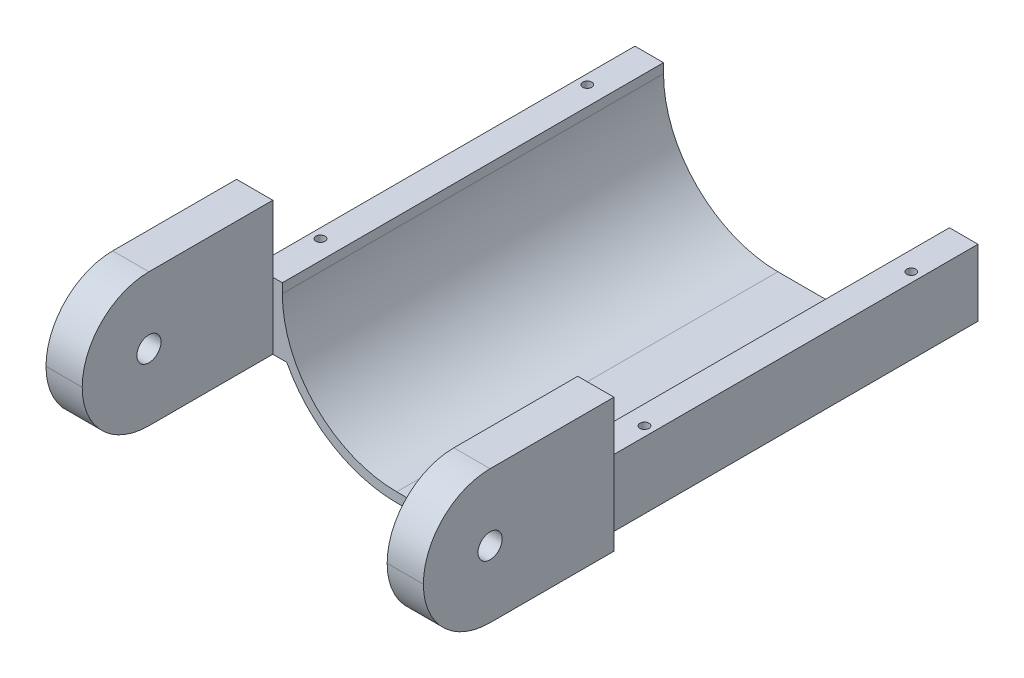
SolidWorks part; units mm, degrees
ref_plane "Front Plane" through (0, 0, 0) normal (0, 0, 1) x (1, 0, 0)
ref_plane "Top Plane" through (0, 0, 0) normal (0, 1, 0) x (1, 0, 0)
ref_plane "Right Plane" through (0, 0, 0) normal (1, 0, 0) x (0, 0, -1)
sketch "Sketch1" plane through (0, 0, 0) normal (0, 0, 1) x (1, 0, 0)
  line L1 (60, 0) -> (90, 0)
  line L2 (0, 60) -> (0, 65)
  line L4 (150, 60) -> (150, 65)
  line L5 (-5, 60) -> (-5, 65)
  line L6 (60, -5) -> (90, -5)
  line L7 (155, 60) -> (155, 65)
  line L8 (-5, 65) -> (155, 65)
  line L10 (-5, 60) -> (-15, 60)
  line L11 (-5, 60) -> (-5, 65)
  line L12 (-5, 65) -> (-15, 65)
  line L13 (-15, 60) -> (-15, 65)
  line L14 (155, 60) -> (165, 60)
  line L15 (155, 60) -> (155, 65)
  line L16 (155, 65) -> (165, 65)
  line L17 (165, 60) -> (165, 65)
  arc A0 (90, 0) -> (150, 60) centre (90, 60) ccw
  arc A1 (60, 0) -> (0, 60) centre (60, 60) cw
  arc A2 (60, -5) -> (-5, 60) centre (60, 60) cw
  arc A3 (90, -5) -> (155, 60) centre (90, 60) ccw
  point P12 (0, 0)
  dimension "D4" = 60
  dimension "D1" = 5
  dimension "D2" = 10
  dimension "D3" = 10
extrude "Boss-Extrude1" add sketch "Sketch1" along normal blind 200 contours L13 L10 L5 L12 | L6 A3 L7 L8 L4 A0 L1 A1 L2 L5 A2 | L14 L17 L16 L7
sketch "Sketch2" plane through (0, 65, 0) normal (0, 1, 0) x (1, 0, 0)
  line L0 (0, 0) -> (-15, 0) construction
  line L1 (-15, -200) -> (-5, -200)
  line L2 (-15, -200) -> (-15, 0)
  line L3 (-15, 0) -> (-5, 0)
  line L4 (-5, -200) -> (-5, 0)
  line L5 (150, -200) -> (165, -200) construction
  line L6 (165, 0) -> (155, 0)
  line L7 (165, 0) -> (165, -200)
  line L8 (165, -200) -> (155, -200)
  line L9 (155, 0) -> (155, -200)
  line L10 (160, -200) -> (160, 0)
  line L11 (160, 0) -> (-10, 0)
  line L12 (-10, 0) -> (-10, -200)
  circle A0 centre (-10, -170) radius 2.3813
  circle A1 centre (-10, -30) radius 2.3813
  circle A2 centre (160, -30) radius 2.3813
  circle A3 centre (160, -170) radius 2.3813
  dimension "D3" = 4.7625
  dimension "D4" = 4.7625
  dimension "D5" = 4.7625
  dimension "D6" = 4.7625
  dimension "D1" = 10
  dimension "D2" = 10
  dimension "D7" = 30
  dimension "D8" = 30
  dimension "D9" = 30
  dimension "D10" = 30
extrude "Cut-Extrude1" cut sketch "Sketch2" against normal blind 200 contours A1 | A0 | A3 | A2
sketch "Sketch3" plane through (0, 0, 200) normal (0, 0, 1) x (1, 0, 0)
  line L1 (-5, 60) -> (-15, 60)
  line L2 (-5, 60) -> (-5, 70)
  line L3 (-5, 70) -> (-15, 70)
  line L4 (-15, 60) -> (-15, 70)
  line L5 (-15, 70) -> (-5, 70)
  line L6 (-15, 70) -> (-15, 100)
  line L7 (-15, 100) -> (-5, 100)
  line L8 (-5, 70) -> (-5, 100)
  line L9 (-15, 60) -> (-5, 60)
  line L10 (-15, 60) -> (-15, 30)
  line L11 (-15, 30) -> (-5, 30)
  line L12 (-5, 60) -> (-5, 30)
  line M4 (-15, 65) -> (-15, 60)
  line M5 (-15, 60) -> (-5, 60)
  line M17 (0, 65) -> (-15, 65)
  dimension "D1" = 10
  dimension "D2" = 30
  dimension "D3" = 30
extrude "Boss-Extrude2" add sketch "Sketch3" along normal blind 100 contours L12 L10 L11 M5 | L2 M5 M17 M4 | L4 L2 L3 M17 | L3 L8 L7 L6
sketch "Sketch4" plane through (-5, 0, 0) normal (1, 0, 0) x (0, 0, -1)
  line L0 (-300, 100) -> (-200, 100) construction
  line L1 (-265.01, 30) -> (-230, 30)
  line L2 (-300, 64.99) -> (-300, 65.01)
  line L3 (-265.01, 100) -> (-230, 100)
  line L4 (-230, 30) -> (-230, 100)
  line L5 (-230, 100) -> (-300, 30)
  circle A0 centre (-265, 65) radius 6.35
  arc A1 (-300, 65.01) -> (-265.01, 100) centre (-265.01, 65.01) cw
  arc A2 (-265.01, 30) -> (-300, 64.99) centre (-265.01, 64.99) cw
  line M6 (-200, 100) -> (-300, 100)
  line M7 (-300, 100) -> (-300, 30)
  line M8 (-300, 30) -> (-200, 30)
  dimension "D2" = 12.7
  dimension "D3" = 34.99
  dimension "D1" = 70
extrude "Cut-Extrude2" cut sketch "Sketch4" against normal blind 100 contours L5 A0 | L5 A0 | A2 L5 M8 | L5 A2 M7 | A1 M7 M6
sketch "Sketch5" plane through (165, 0, 0) normal (1, 0, 0) x (0, 0, -1)
  line L6 (-300, 65.01) -> (-300, 64.99)
  line L7 (-265.01, 30) -> (-200, 30)
  line L8 (-200, 30) -> (-200, 60)
  line L9 (-200, 60) -> (-200, 65)
  line L10 (-200, 65) -> (-200, 100)
  line L11 (-200, 100) -> (-265.01, 100)
  line L12 (-300, 65.01) -> (-300, 64.99)
  line L13 (-265.01, 30) -> (-200, 30)
  line L14 (-200, 30) -> (-200, 60)
  line L15 (-200, 60) -> (-200, 65)
  line L16 (-200, 65) -> (-200, 100)
  line L17 (-200, 100) -> (-265.01, 100)
  circle A0 centre (-265, 65) radius 6.35 construction
  circle A1 centre (-265, 65) radius 6.35
  arc A2 (-265.01, 100) -> (-300, 65.01) centre (-265.01, 65.01) ccw
  arc A3 (-300, 64.99) -> (-265.01, 30) centre (-265.01, 64.99) ccw
  arc A4 (-265.01, 100) -> (-300, 65.01) centre (-265.01, 65.01) ccw
  arc A5 (-300, 64.99) -> (-265.01, 30) centre (-265.01, 64.99) ccw
  dimension "D1" = 0
extrude "Boss-Extrude5" add sketch "Sketch5" against normal up to vertex
sketch "Sketch6" plane through (-5, 0, 0) normal (1, 0, 0) x (0, 0, -1)
  line L6 (-300, 65.01) -> (-300, 64.99)
  line L7 (-265.01, 30) -> (-200, 30)
  line L8 (-200, 30) -> (-200, 60)
  line L9 (-200, 60) -> (-200, 65)
  line L10 (-200, 65) -> (-200, 100)
  line L11 (-200, 100) -> (-265.01, 100)
  line L12 (-300, 65.01) -> (-300, 64.99)
  line L13 (-265.01, 30) -> (-200, 30)
  line L14 (-200, 30) -> (-200, 60)
  line L15 (-200, 60) -> (-200, 65)
  line L16 (-200, 65) -> (-200, 100)
  line L17 (-200, 100) -> (-265.01, 100)
  circle A0 centre (-265, 65) radius 6.35 construction
  circle A1 centre (-265, 65) radius 6.35
  arc A2 (-265.01, 100) -> (-300, 65.01) centre (-265.01, 65.01) ccw
  arc A3 (-300, 64.99) -> (-265.01, 30) centre (-265.01, 64.99) ccw
  arc A4 (-265.01, 100) -> (-300, 65.01) centre (-265.01, 65.01) ccw
  arc A5 (-300, 64.99) -> (-265.01, 30) centre (-265.01, 64.99) ccw
  dimension "D1" = 0
extrude "Boss-Extrude6" add sketch "Sketch6" along normal up to vertex
sketch "Sketch7" plane through (0, 0, 0) normal (0, 0, -1) x (-1, 0, 0)
  line L0 (-165, 30) -> (-145.0237, 30)
  line L1 (-145.0237, 30) -> (5, 30)
  line L2 (5, 30) -> (-150, 30)
  line L4 (15, 60) -> (5, 60)
  line L5 (0, 35) -> (0, 30)
  line L6 (0, 30) -> (15, 30)
  line L7 (15, 30) -> (15, 60)
  line L8 (15, 60) -> (5, 60)
  line L9 (0, 35) -> (0, 30)
  line L10 (0, 30) -> (15, 30)
  line L11 (15, 30) -> (15, 60)
  line L12 (-155, 60) -> (-165, 60)
  line L13 (-165, 60) -> (-165, 30)
  line L14 (-165, 30) -> (-150, 30)
  line L15 (-150, 30) -> (-150, 35)
  line L16 (-155, 60) -> (-165, 60)
  line L17 (-165, 60) -> (-165, 30)
  line L18 (-165, 30) -> (-150, 30)
  line L19 (-150, 30) -> (-150, 35)
  arc A1 (0, 35) -> (5, 60) centre (-60, 60) ccw
  arc A2 (0, 35) -> (5, 60) centre (-60, 60) ccw
  arc A3 (-155, 60) -> (-150, 35) centre (-90, 60) ccw
  arc A4 (-155, 60) -> (-150, 35) centre (-90, 60) ccw
  line M20 (-165, 60) -> (-155, 60)
  arc M21 (-155, 60) -> (-90, -5) centre (-90, 60) ccw
  arc M23 (-60, -5) -> (5, 60) centre (-60, 60) ccw
  line M24 (5, 60) -> (15, 60)
  dimension "D1" = 0
  dimension "D2" = 0
extrude "Boss-Extrude7" add sketch "Sketch7" against normal up to vertex contours L19 L0 M21 | L0 L19 L17 M21 M20 | L9 L1 M23 | L10 L11 L9 L2 M24 M23
sketch "Sketch8" plane through (165, 0, 0) normal (1, 0, 0) x (0, 0, -1)
  line L0 (-200, 100) -> (-200, 30)
  line L6 (-265.01, 30) -> (0, 30)
  line L7 (0, 30) -> (0, 65)
  line L8 (0, 65) -> (-200, 65)
  line L9 (-200, 65) -> (-200, 100)
  line L10 (-200, 100) -> (-265.01, 100)
  line L11 (-300, 65.01) -> (-300, 64.99)
  line L12 (-265.01, 30) -> (0, 30)
  line L13 (0, 30) -> (0, 65)
  line L14 (0, 65) -> (-200, 65)
  line L15 (-200, 65) -> (-200, 100)
  line L16 (-200, 100) -> (-265.01, 100)
  line L17 (-300, 65.01) -> (-300, 64.99)
  circle A0 centre (-265, 65) radius 6.35 construction
  circle A1 centre (-265, 65) radius 6.35
  arc A2 (-265.01, 100) -> (-300, 65.01) centre (-265.01, 65.01) ccw
  arc A3 (-300, 64.99) -> (-265.01, 30) centre (-265.01, 64.99) ccw
  arc A4 (-265.01, 100) -> (-300, 65.01) centre (-265.01, 65.01) ccw
  arc A5 (-300, 64.99) -> (-265.01, 30) centre (-265.01, 64.99) ccw
  line M10 (-265.01, 30) -> (0, 30)
  line M13 (-200, 65) -> (-200, 100)
  line M14 (-200, 100) -> (-265.01, 100)
  arc M15 (-265.01, 100) -> (-300, 65.01) centre (-265.01, 65.01) ccw
  line M16 (-300, 65.01) -> (-300, 64.99)
  arc M17 (-300, 64.99) -> (-265.01, 30) centre (-265.01, 64.99) ccw
  circle M18 centre (-265, 65) radius 6.35
  dimension "D1" = 0
extrude "Boss-Extrude8" add sketch "Sketch8" along normal blind 9 contours L0 M13 M14 M15 M16 M17 M10 M18
sketch "Sketch9" plane through (-15, 0, 0) normal (-1, 0, 0) x (0, 0, 1)
  line L0 (200, 100) -> (200, 30)
  line L6 (0, 65) -> (0, 30)
  line L7 (0, 30) -> (265.01, 30)
  line L8 (300, 64.99) -> (300, 65.01)
  line L9 (265.01, 100) -> (200, 100)
  line L10 (200, 100) -> (200, 65)
  line L11 (200, 65) -> (0, 65)
  line L12 (0, 65) -> (0, 30)
  line L13 (0, 30) -> (265.01, 30)
  line L14 (300, 64.99) -> (300, 65.01)
  line L15 (265.01, 100) -> (200, 100)
  line L16 (200, 100) -> (200, 65)
  line L17 (200, 65) -> (0, 65)
  circle A0 centre (265, 65) radius 6.35 construction
  circle A1 centre (265, 65) radius 6.35
  arc A2 (265.01, 30) -> (300, 64.99) centre (265.01, 64.99) ccw
  arc A3 (300, 65.01) -> (265.01, 100) centre (265.01, 65.01) ccw
  arc A4 (265.01, 30) -> (300, 64.99) centre (265.01, 64.99) ccw
  arc A5 (300, 65.01) -> (265.01, 100) centre (265.01, 65.01) ccw
  line M11 (0, 30) -> (265.01, 30)
  arc M12 (265.01, 30) -> (300, 64.99) centre (265.01, 64.99) ccw
  line M13 (300, 64.99) -> (300, 65.01)
  arc M14 (300, 65.01) -> (265.01, 100) centre (265.01, 65.01) ccw
  line M15 (265.01, 100) -> (200, 100)
  line M16 (200, 100) -> (200, 65)
  circle M18 centre (265, 65) radius 6.35
  dimension "D1" = 0
extrude "Boss-Extrude9" add sketch "Sketch9" along normal blind 9 contours L0 M16 M11 M12 M13 M14 M15 M18
sketch "Sketch10" plane through (150, 0, 0) normal (-1, 0, 0) x (0, 0, 1)
  line L0 (200, 60) -> (200, 65)
  line L8 (0, 65) -> (0, 60)
  line L9 (0, 60) -> (200, 60)
  line L10 (200, 60) -> (200, 30)
  line L11 (200, 30) -> (265.01, 30)
  line L12 (300, 64.99) -> (300, 65.01)
  line L13 (265.01, 100) -> (200, 100)
  line L14 (200, 100) -> (200, 65)
  line L15 (200, 65) -> (0, 65)
  line L16 (0, 65) -> (0, 60)
  line L17 (0, 60) -> (200, 60)
  line L18 (200, 60) -> (200, 30)
  line L19 (200, 30) -> (265.01, 30)
  line L20 (300, 64.99) -> (300, 65.01)
  line L21 (265.01, 100) -> (200, 100)
  line L22 (200, 100) -> (200, 65)
  line L23 (200, 65) -> (0, 65)
  circle A0 centre (265, 65) radius 6.35 construction
  circle A1 centre (265, 65) radius 6.35
  arc A2 (265.01, 30) -> (300, 64.99) centre (265.01, 64.99) ccw
  arc A3 (300, 65.01) -> (265.01, 100) centre (265.01, 65.01) ccw
  arc A4 (265.01, 30) -> (300, 64.99) centre (265.01, 64.99) ccw
  arc A5 (300, 65.01) -> (265.01, 100) centre (265.01, 65.01) ccw
  line M14 (200, 60) -> (200, 30)
  line M15 (200, 30) -> (265.01, 30)
  arc M16 (265.01, 30) -> (300, 64.99) centre (265.01, 64.99) ccw
  line M17 (300, 64.99) -> (300, 65.01)
  arc M18 (300, 65.01) -> (265.01, 100) centre (265.01, 65.01) ccw
  line M19 (265.01, 100) -> (200, 100)
  line M20 (200, 100) -> (200, 65)
  circle M22 centre (265, 65) radius 6.35
  dimension "D1" = 0
extrude "Cut-Extrude3" cut sketch "Sketch10" against normal blind 5 contours L0 M14 M15 M16 M17 M18 M19 M20 M22
sketch "Sketch11" plane through (0, 0, 0) normal (1, 0, 0) x (0, 0, -1)
  line L0 (-200, 60) -> (-200, 65)
  line L8 (0, 60) -> (0, 65)
  line L9 (0, 65) -> (-200, 65)
  line L10 (-200, 65) -> (-200, 100)
  line L11 (-200, 100) -> (-265.01, 100)
  line L12 (-300, 65.01) -> (-300, 64.99)
  line L13 (-265.01, 30) -> (-200, 30)
  line L14 (-200, 30) -> (-200, 60)
  line L15 (-200, 60) -> (0, 60)
  line L16 (0, 60) -> (0, 65)
  line L17 (0, 65) -> (-200, 65)
  line L18 (-200, 65) -> (-200, 100)
  line L19 (-200, 100) -> (-265.01, 100)
  line L20 (-300, 65.01) -> (-300, 64.99)
  line L21 (-265.01, 30) -> (-200, 30)
  line L22 (-200, 30) -> (-200, 60)
  line L23 (-200, 60) -> (0, 60)
  arc A2 (-265.01, 100) -> (-300, 65.01) centre (-265.01, 65.01) ccw
  arc A3 (-300, 64.99) -> (-265.01, 30) centre (-265.01, 64.99) ccw
  arc A4 (-265.01, 100) -> (-300, 65.01) centre (-265.01, 65.01) ccw
  arc A5 (-300, 64.99) -> (-265.01, 30) centre (-265.01, 64.99) ccw
  line M13 (-200, 65) -> (-200, 100)
  line M14 (-200, 100) -> (-265.01, 100)
  arc M15 (-265.01, 100) -> (-300, 65.01) centre (-265.01, 65.01) ccw
  line M16 (-300, 65.01) -> (-300, 64.99)
  arc M17 (-300, 64.99) -> (-265.01, 30) centre (-265.01, 64.99) ccw
  line M18 (-265.01, 30) -> (-200, 30)
  line M19 (-200, 30) -> (-200, 60)
  circle M21 centre (-265, 65) radius 6.35
  dimension "D1" = 0
extrude "Cut-Extrude4" cut sketch "Sketch11" against normal blind 5 contours L0 M19 M13 M14 M15 M16 M17 M18 M21
sketch "Sketch12" plane through (0, 60, 0) normal (0, 1, 0) x (1, 0, 0)
  circle A0 centre (160, -30) radius 2.3813 construction
  circle A1 centre (160, -30) radius 2.3813
  circle A2 centre (-10, -170) radius 2.3813 construction
  circle A3 centre (-10, -170) radius 2.3813
  circle A4 centre (-10, -30) radius 2.3813 construction
  circle A5 centre (-10, -30) radius 2.3813
  circle A6 centre (160, -170) radius 2.3813 construction
  circle A7 centre (160, -170) radius 2.3813
extrude "Cut-Extrude5" cut sketch "Sketch12" against normal through all
